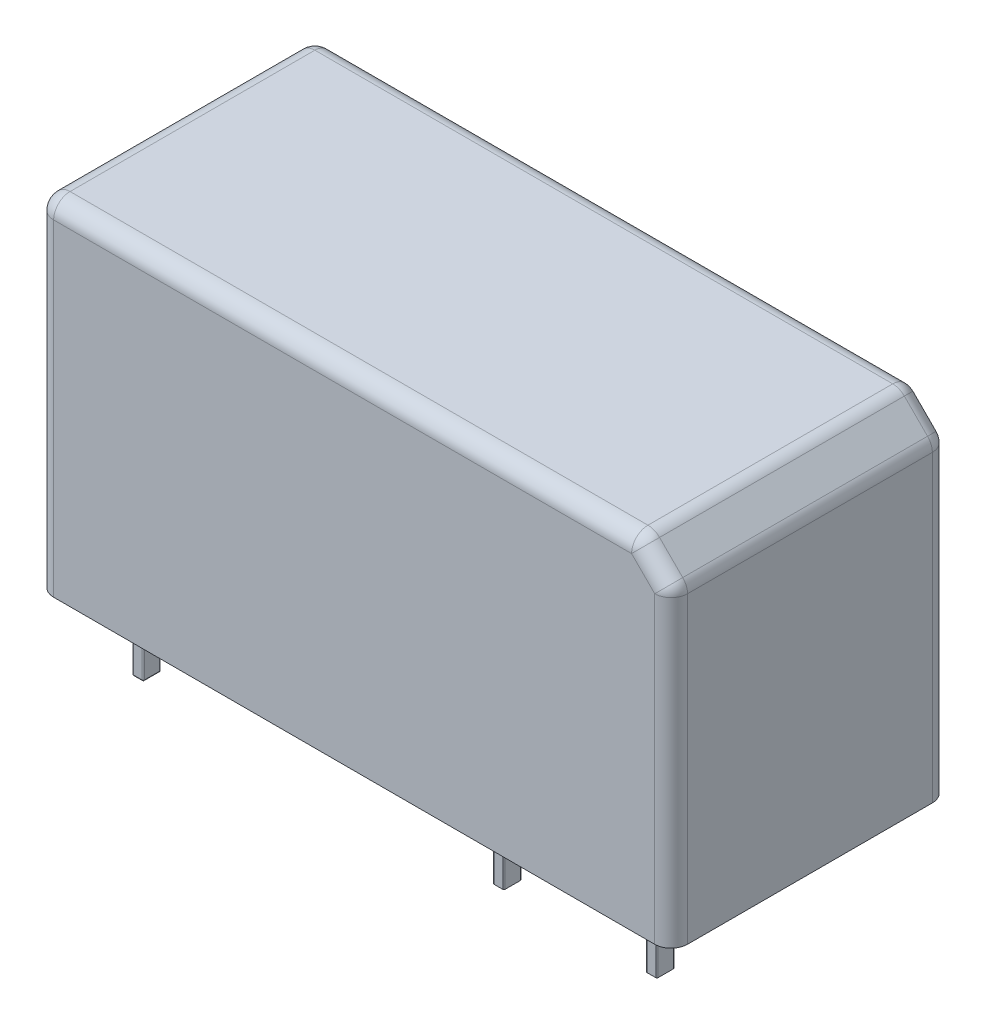
SolidWorks part; units mm, degrees
ref_plane "Спереди" through (0, 0, 0) normal (0, 0, 1) x (1, 0, 0)
ref_plane "Сверху" through (0, 0, 0) normal (0, 1, 0) x (1, 0, 0)
ref_plane "Справа" through (0, 0, 0) normal (1, 0, 0) x (0, 0, -1)
sketch "Эскиз1" plane through (0, 0, 0) normal (0, 1, 0) x (1, 0, 0)
  line L1 (-14.5, -6.35) -> (14.5, -6.35)
  line L2 (-14.5, -6.35) -> (-14.5, 6.35)
  line L3 (-14.5, 6.35) -> (14.5, 6.35)
  line L4 (14.5, -6.35) -> (14.5, 6.35)
  line L5 (-14.5, -6.35) -> (14.5, 6.35) construction
  line L6 (-14.5, 6.35) -> (14.5, -6.35) construction
  point P0 (0, 0)
  dimension "D1" = 29
  dimension "D2" = 12.7
extrude "Бобышка-Вытянуть1" add sketch "Эскиз1" along normal blind 15.7
sketch "Эскиз2" plane through (0, 0, 0) normal (0, -1, 0) x (1, 0, 0)
  line L0 (-14.5, -6.35) -> (-14.5, 6.35) construction
  line L1 (-12.3, 4.15) -> (-11.9, 4.15)
  line L2 (-12.35, 4.1) -> (-12.35, 3.4)
  line L3 (-12.3, 3.35) -> (-11.9, 3.35)
  line L4 (-11.85, 4.1) -> (-11.85, 3.4)
  line L5 (-12.35, 4.15) -> (-11.85, 3.35) construction
  line L6 (-12.35, 3.35) -> (-11.85, 4.15) construction
  line L7 (-7.35, 4.1) -> (-7.35, 3.4) [skipped]
  line L8 (-6.85, 4.1) -> (-6.85, 3.4) [skipped]
  line L9 (-7.3, 4.15) -> (-6.9, 4.15) [skipped]
  line L10 (-7.3, 3.35) -> (-6.9, 3.35) [skipped]
  line L11 (-2.35, 4.1) -> (-2.35, 3.4) [skipped]
  line L12 (-1.85, 4.1) -> (-1.85, 3.4) [skipped]
  line L13 (-2.3, 4.15) -> (-1.9, 4.15) [skipped]
  line L14 (-2.3, 3.35) -> (-1.9, 3.35) [skipped]
  line L27 (-7.35, -3.4) -> (-7.35, -4.1) [skipped]
  line L28 (-6.85, -3.4) -> (-6.85, -4.1) [skipped]
  line L29 (-7.3, -3.35) -> (-6.9, -3.35) [skipped]
  line L30 (-7.3, -4.15) -> (-6.9, -4.15) [skipped]
  line L31 (-2.35, -3.4) -> (-2.35, -4.1) [skipped]
  line L32 (-1.85, -3.4) -> (-1.85, -4.1) [skipped]
  line L33 (-2.3, -3.35) -> (-1.9, -3.35) [skipped]
  line L34 (-2.3, -4.15) -> (-1.9, -4.15) [skipped]
  line L39 (7.65, -3.4) -> (7.65, -4.1)
  line L40 (8.15, -3.4) -> (8.15, -4.1)
  line L41 (7.7, -3.35) -> (8.1, -3.35)
  line L42 (7.7, -4.15) -> (8.1, -4.15)
  line L47 (-12.35, -3.4) -> (-12.35, -4.1)
  line L48 (-11.85, -3.4) -> (-11.85, -4.1)
  line L49 (-12.3, -3.35) -> (-11.9, -3.35)
  line L50 (-12.3, -4.15) -> (-11.9, -4.15)
  line L51 (2.65, 4.1) -> (2.65, 3.4) [skipped]
  line L52 (3.15, 4.1) -> (3.15, 3.4) [skipped]
  line L53 (2.7, 4.15) -> (3.1, 4.15) [skipped]
  line L54 (2.7, 3.35) -> (3.1, 3.35) [skipped]
  line L55 (12.65, 4.1) -> (12.65, 3.4) [skipped]
  line L56 (13.15, 4.1) -> (13.15, 3.4) [skipped]
  line L57 (12.7, 4.15) -> (13.1, 4.15) [skipped]
  line L58 (12.7, 3.35) -> (13.1, 3.35) [skipped]
  line L59 (2.65, -3.4) -> (2.65, -4.1) [skipped]
  line L60 (3.15, -3.4) -> (3.15, -4.1) [skipped]
  line L61 (2.7, -3.35) -> (3.1, -3.35) [skipped]
  line L62 (2.7, -4.15) -> (3.1, -4.15) [skipped]
  line L63 (7.65, 4.1) -> (7.65, 3.4) [skipped]
  line L64 (8.15, 4.1) -> (8.15, 3.4) [skipped]
  line L65 (7.7, 4.15) -> (8.1, 4.15) [skipped]
  line L66 (7.7, 3.35) -> (8.1, 3.35) [skipped]
  line L67 (12.65, -3.4) -> (12.65, -4.1) [skipped]
  line L68 (13.15, -3.4) -> (13.15, -4.1) [skipped]
  line L69 (12.7, -3.35) -> (13.1, -3.35) [skipped]
  line L70 (12.7, -4.15) -> (13.1, -4.15) [skipped]
  line L71 (11.15, 4.15) -> (11.65, 3.35) construction
  line L72 (11.2, 4.15) -> (11.6, 4.15)
  line L73 (11.15, 3.35) -> (11.65, 4.15) construction
  line L74 (11.15, 4.1) -> (11.15, 3.4)
  line L75 (11.65, 4.1) -> (11.65, 3.4)
  line L76 (11.2, 3.35) -> (11.6, 3.35)
  line L77 (4.15, 4.15) -> (4.65, 3.35) construction
  line L78 (4.2, 4.15) -> (4.6, 4.15)
  line L79 (4.2, 3.35) -> (4.6, 3.35)
  line L80 (4.15, 4.1) -> (4.15, 3.4)
  line L81 (4.65, 4.1) -> (4.65, 3.4)
  line L82 (4.15, 3.35) -> (4.65, 4.15) construction
  line L83 (-12.1, 3.75) -> (12.9, 3.75) construction
  arc A0 (-12.35, 3.4) -> (-12.3, 3.35) centre (-12.3, 3.4) ccw
  arc A1 (-11.9, 3.35) -> (-11.85, 3.4) centre (-11.9, 3.4) ccw
  arc A2 (-11.9, 4.15) -> (-11.85, 4.1) centre (-11.9, 4.1) cw
  arc A3 (-12.3, 4.15) -> (-12.35, 4.1) centre (-12.3, 4.1) ccw
  arc A4 (-7.35, 3.4) -> (-7.3, 3.35) centre (-7.3, 3.4) ccw [skipped]
  arc A5 (-6.9, 3.35) -> (-6.85, 3.4) centre (-6.9, 3.4) ccw [skipped]
  arc A6 (-6.9, 4.15) -> (-6.85, 4.1) centre (-6.9, 4.1) cw [skipped]
  arc A7 (-7.3, 4.15) -> (-7.35, 4.1) centre (-7.3, 4.1) ccw [skipped]
  arc A8 (-2.35, 3.4) -> (-2.3, 3.35) centre (-2.3, 3.4) ccw [skipped]
  arc A9 (-1.9, 3.35) -> (-1.85, 3.4) centre (-1.9, 3.4) ccw [skipped]
  arc A10 (-1.9, 4.15) -> (-1.85, 4.1) centre (-1.9, 4.1) cw [skipped]
  arc A11 (-2.3, 4.15) -> (-2.35, 4.1) centre (-2.3, 4.1) ccw [skipped]
  arc A24 (-7.35, -4.1) -> (-7.3, -4.15) centre (-7.3, -4.1) ccw [skipped]
  arc A25 (-6.9, -4.15) -> (-6.85, -4.1) centre (-6.9, -4.1) ccw [skipped]
  arc A26 (-6.9, -3.35) -> (-6.85, -3.4) centre (-6.9, -3.4) cw [skipped]
  arc A27 (-7.3, -3.35) -> (-7.35, -3.4) centre (-7.3, -3.4) ccw [skipped]
  arc A28 (-2.35, -4.1) -> (-2.3, -4.15) centre (-2.3, -4.1) ccw [skipped]
  arc A29 (-1.9, -4.15) -> (-1.85, -4.1) centre (-1.9, -4.1) ccw [skipped]
  arc A30 (-1.9, -3.35) -> (-1.85, -3.4) centre (-1.9, -3.4) cw [skipped]
  arc A31 (-2.3, -3.35) -> (-2.35, -3.4) centre (-2.3, -3.4) ccw [skipped]
  arc A36 (7.65, -4.1) -> (7.7, -4.15) centre (7.7, -4.1) ccw
  arc A37 (8.1, -4.15) -> (8.15, -4.1) centre (8.1, -4.1) ccw
  arc A38 (8.1, -3.35) -> (8.15, -3.4) centre (8.1, -3.4) cw
  arc A39 (7.7, -3.35) -> (7.65, -3.4) centre (7.7, -3.4) ccw
  arc A44 (-12.35, -4.1) -> (-12.3, -4.15) centre (-12.3, -4.1) ccw
  arc A45 (-11.9, -4.15) -> (-11.85, -4.1) centre (-11.9, -4.1) ccw
  arc A46 (-11.9, -3.35) -> (-11.85, -3.4) centre (-11.9, -3.4) cw
  arc A47 (-12.3, -3.35) -> (-12.35, -3.4) centre (-12.3, -3.4) ccw
  arc A48 (2.65, 3.4) -> (2.7, 3.35) centre (2.7, 3.4) ccw [skipped]
  arc A49 (3.1, 3.35) -> (3.15, 3.4) centre (3.1, 3.4) ccw [skipped]
  arc A50 (3.1, 4.15) -> (3.15, 4.1) centre (3.1, 4.1) cw [skipped]
  arc A51 (2.7, 4.15) -> (2.65, 4.1) centre (2.7, 4.1) ccw [skipped]
  arc A52 (12.65, 3.4) -> (12.7, 3.35) centre (12.7, 3.4) ccw [skipped]
  arc A53 (13.1, 3.35) -> (13.15, 3.4) centre (13.1, 3.4) ccw [skipped]
  arc A54 (13.1, 4.15) -> (13.15, 4.1) centre (13.1, 4.1) cw [skipped]
  arc A55 (12.7, 4.15) -> (12.65, 4.1) centre (12.7, 4.1) ccw [skipped]
  arc A56 (2.65, -4.1) -> (2.7, -4.15) centre (2.7, -4.1) ccw [skipped]
  arc A57 (3.1, -4.15) -> (3.15, -4.1) centre (3.1, -4.1) ccw [skipped]
  arc A58 (3.1, -3.35) -> (3.15, -3.4) centre (3.1, -3.4) cw [skipped]
  arc A59 (2.7, -3.35) -> (2.65, -3.4) centre (2.7, -3.4) ccw [skipped]
  arc A60 (12.7, -3.35) -> (12.65, -3.4) centre (12.7, -3.4) ccw [skipped]
  arc A61 (7.65, 3.4) -> (7.7, 3.35) centre (7.7, 3.4) ccw [skipped]
  arc A62 (8.1, 3.35) -> (8.15, 3.4) centre (8.1, 3.4) ccw [skipped]
  arc A63 (8.1, 4.15) -> (8.15, 4.1) centre (8.1, 4.1) cw [skipped]
  arc A64 (7.7, 4.15) -> (7.65, 4.1) centre (7.7, 4.1) ccw [skipped]
  arc A65 (12.65, -4.1) -> (12.7, -4.15) centre (12.7, -4.1) ccw [skipped]
  arc A66 (13.1, -4.15) -> (13.15, -4.1) centre (13.1, -4.1) ccw [skipped]
  arc A67 (13.1, -3.35) -> (13.15, -3.4) centre (13.1, -3.4) cw [skipped]
  arc A68 (11.6, 3.35) -> (11.65, 3.4) centre (11.6, 3.4) ccw
  arc A69 (11.15, 3.4) -> (11.2, 3.35) centre (11.2, 3.4) ccw
  arc A70 (11.2, 4.15) -> (11.15, 4.1) centre (11.2, 4.1) ccw
  arc A71 (11.6, 4.15) -> (11.65, 4.1) centre (11.6, 4.1) cw
  arc A72 (4.15, 3.4) -> (4.2, 3.35) centre (4.2, 3.4) ccw
  arc A73 (4.6, 3.35) -> (4.65, 3.4) centre (4.6, 3.4) ccw
  arc A74 (4.2, 4.15) -> (4.15, 4.1) centre (4.2, 4.1) ccw
  arc A75 (4.6, 4.15) -> (4.65, 4.1) centre (4.6, 4.1) cw
  point P0 (-12.1, 3.75)
  point P8 (-14.5, 0)
  point P21 (-11.85, 3.75)
  point P22 (11.4, 3.75)
  point P63 (11.65, 3.75)
  point P64 (4.4, 3.75)
  point P81 (4.65, 3.75)
  point P109 (4.15, 3.75)
  point P110 (11.15, 3.75)
  dimension "D1" = 0.05
  dimension "D2" = 0.5
  dimension "D3" = 3.75
  dimension "D4" = 2.4
  dimension "D5" = 0.8
  dimension "D8" = 0.8
  dimension "D9" = 0.8
  dimension "D10" = 0.5
  dimension "D11" = 0.5
  dimension "D6" = 6
  dimension "D7" = 2
extrude "Бобышка-Вытянуть2" add sketch "Эскиз2" along normal blind 3.5
fillet "Скругление1" radius 0.05 24 edges at (-11.8646, -3.5, 3.3646) (-12.1, -3.5, 3.35) (-12.3354, -3.5, 3.3646) (-12.35, -3.5, 3.75) (-12.3354, -3.5, 4.1354) (-12.1, -3.5, 4.15) (-11.8646, -3.5, 4.1354) (-11.8646, -3.5, -4.1354) (-12.1, -3.5, -4.15) (-12.3354, -3.5, -4.1354) (-12.35, -3.5, -3.75) (-12.3354, -3.5, -3.3646) (-12.1, -3.5, -3.35) (-11.8646, -3.5, -3.3646) (8.1354, -3.5, -4.1354) (7.9, -3.5, -4.15) (7.6646, -3.5, -4.1354) (7.65, -3.5, -3.75) (7.6646, -3.5, -3.3646) (7.9, -3.5, -3.35) (8.1354, -3.5, -3.3646) (-11.85, -3.5, 3.75) (-11.85, -3.5, -3.75) (8.15, -3.5, -3.75)
chamfer "Фаска1" distance 1.5 angle 45 1 edges at (14.5, 15.7, 0)
fillet "Скругление2" radius 0.75 11 edges at (13.75, 14.95, -6.35) (-14.5, 7.85, 6.35) (-14.5, 7.85, -6.35) (14.5, 7.1, -6.35) (14.5, 7.1, 6.35) (13.75, 14.95, 6.35) (14.5, 14.2, 0) (13, 15.7, 0) (-0.75, 15.7, -6.35) (-14.5, 15.7, 0) (-0.75, 15.7, 6.35)
